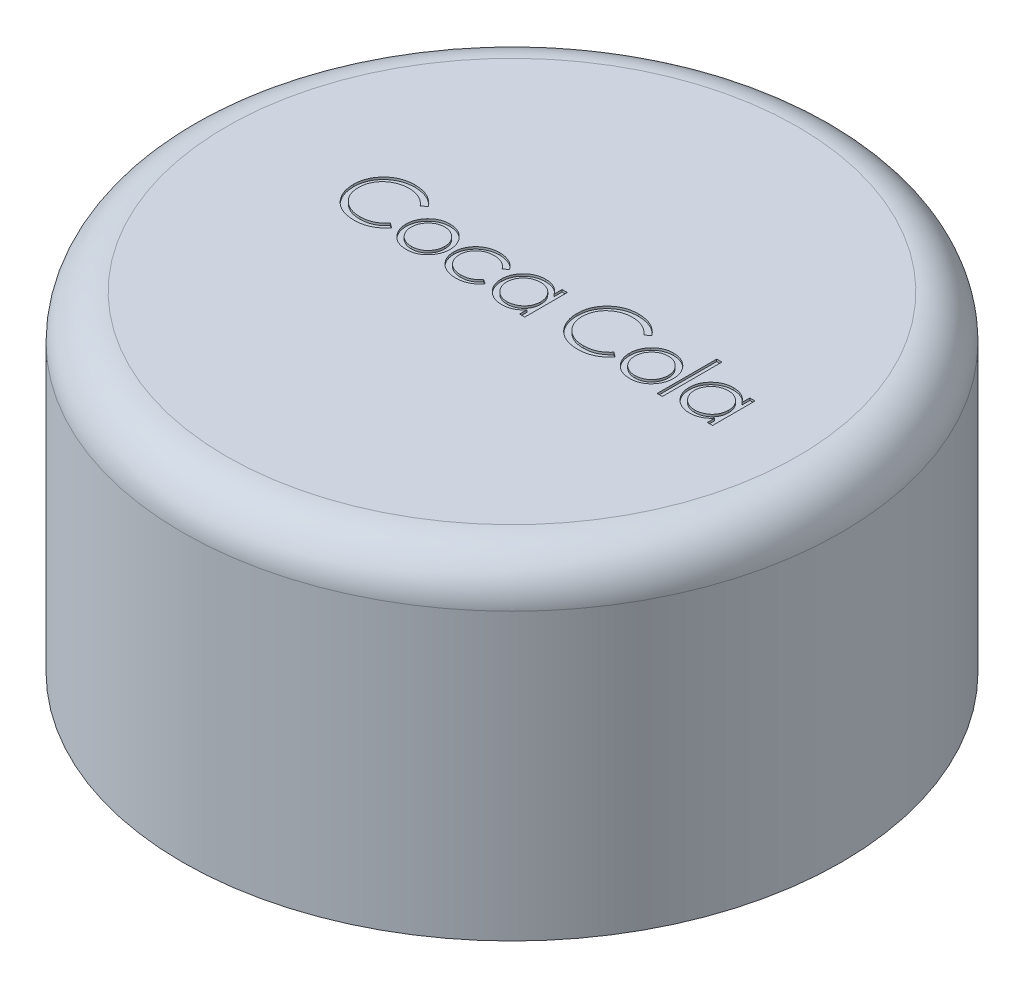
SolidWorks part; units mm, degrees
ref_plane "Alzado" through (0, 0, 0) normal (0, 0, 1) x (1, 0, 0)
ref_plane "Planta" through (0, 0, 0) normal (0, 1, 0) x (1, 0, 0)
ref_plane "Vista lateral" through (0, 0, 0) normal (1, 0, 0) x (0, 0, -1)
sketch "Croquis1" plane through (0, 0, 0) normal (0, 1, 0) x (1, 0, 0)
  circle A0 centre (0, 0) radius 15
  circle A1 centre (0, 0) radius 13.85
  dimension "D1" = 30
  dimension "D2" = 1.15
extrude "Saliente-Extruir1" add sketch "Croquis1" along normal mid plane 15
sketch "Croquis2" plane through (0, 7.5, 0) normal (0, 1, 0) x (1, 0, 0)
  circle A0 centre (0, 0) radius 15
  dimension "D1" = 30
extrude "Saliente-Extruir2" add sketch "Croquis2" against normal blind 2.15
fillet "Redondeo1" radius 2 1 edges at (0, 7.5, 15)
sketch "Croquis3" plane through (0, 7.5, 0) normal (0, 1, 0) x (1, 0, 0)
  text T0 "Coca Cola" font "Century Gothic" height in points 10
extrude "Cortar-Extruir1" cut sketch "Croquis3" against normal blind 0.1
